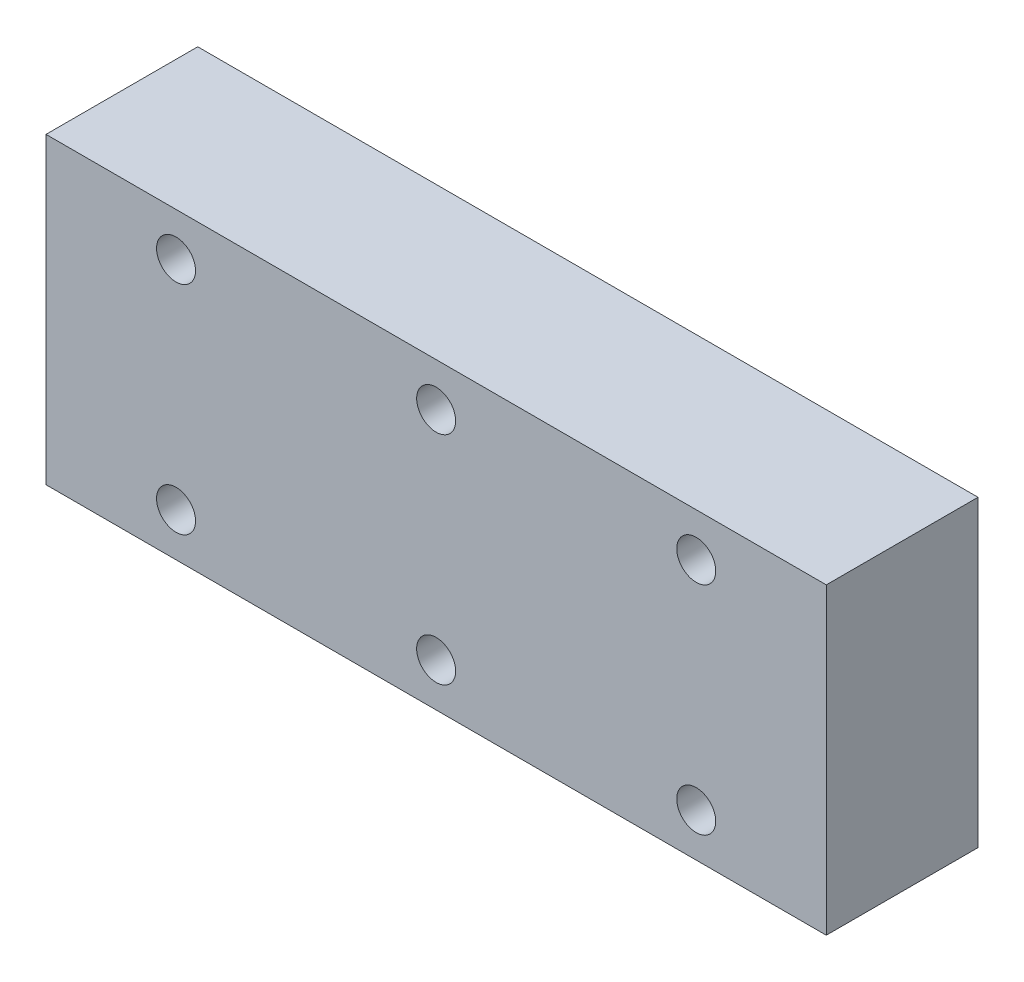
SolidWorks part; units mm, degrees
ref_plane "Alzado" through (0, 0, 0) normal (0, 0, 1) x (1, 0, 0)
ref_plane "Planta" through (0, 0, 0) normal (0, 1, 0) x (1, 0, 0)
ref_plane "Vista lateral" through (0, 0, 0) normal (1, 0, 0) x (0, 0, -1)
sketch "Croquis1" plane through (0, 0, 0) normal (0, 0, 1) x (1, 0, 0)
  line L0 (0, 1.5) -> (0, -1.5)
  line L1 (-9, 3.5) -> (9, 3.5)
  line L2 (-9, 3.5) -> (-9, -3.5)
  line L3 (-9, -3.5) -> (9, -3.5)
  line L4 (9, 3.5) -> (9, -3.5)
  line L5 (-9, 3.5) -> (9, -3.5) construction
  line L6 (-9, -3.5) -> (9, 3.5) construction
  point P0 (0, 0)
  point P9 (0, 0)
  dimension "D1" = 18
  dimension "D2" = 7
  dimension "D3" = 3
extrude "Saliente-Extruir1" add sketch "Croquis1" along normal blind 3.5
sketch "Croquis2" plane through (0, 0, 3.5) normal (0, 0, 1) x (1, 0, 0)
  line L0 (0, 0) -> (-6, 0) construction
  line L1 (0, 0) -> (6, 0) construction
  line L2 (-6, 2.5) -> (-6, -2.5) construction
  line L3 (6, 2.5) -> (6, -2.5) construction
  line L4 (0, 1.6) -> (0, -1.6) construction
  line L5 (0, 2.5) -> (0, -2.5) construction
  circle A0 centre (-6, 2.5) radius 0.45
  circle A1 centre (-6, -2.5) radius 0.45
  circle A2 centre (6, 2.5) radius 0.45
  circle A3 centre (6, -2.5) radius 0.45
  circle A4 centre (0, 2.5) radius 0.45
  circle A5 centre (0, -2.5) radius 0.45
  point P7 (-6, 0)
  point P10 (6, 0)
  point P12 (0, 0)
  point P20 (0, 0)
  dimension "D6" = 0.9
  dimension "D7" = 0.9
  dimension "D8" = 0.9
  dimension "D9" = 0.9
  dimension "D11" = 0.9
  dimension "D12" = 0.9
  dimension "D1" = 6
  dimension "D2" = 6
  dimension "D3" = 3.2
  dimension "D4" = 5
  dimension "D5" = 5
  dimension "D10" = 5
extrude "Cortar-Extruir1" cut sketch "Croquis2" against normal blind 5.75 contours A1 | A4 | A5 | A3 | A2 | A0
